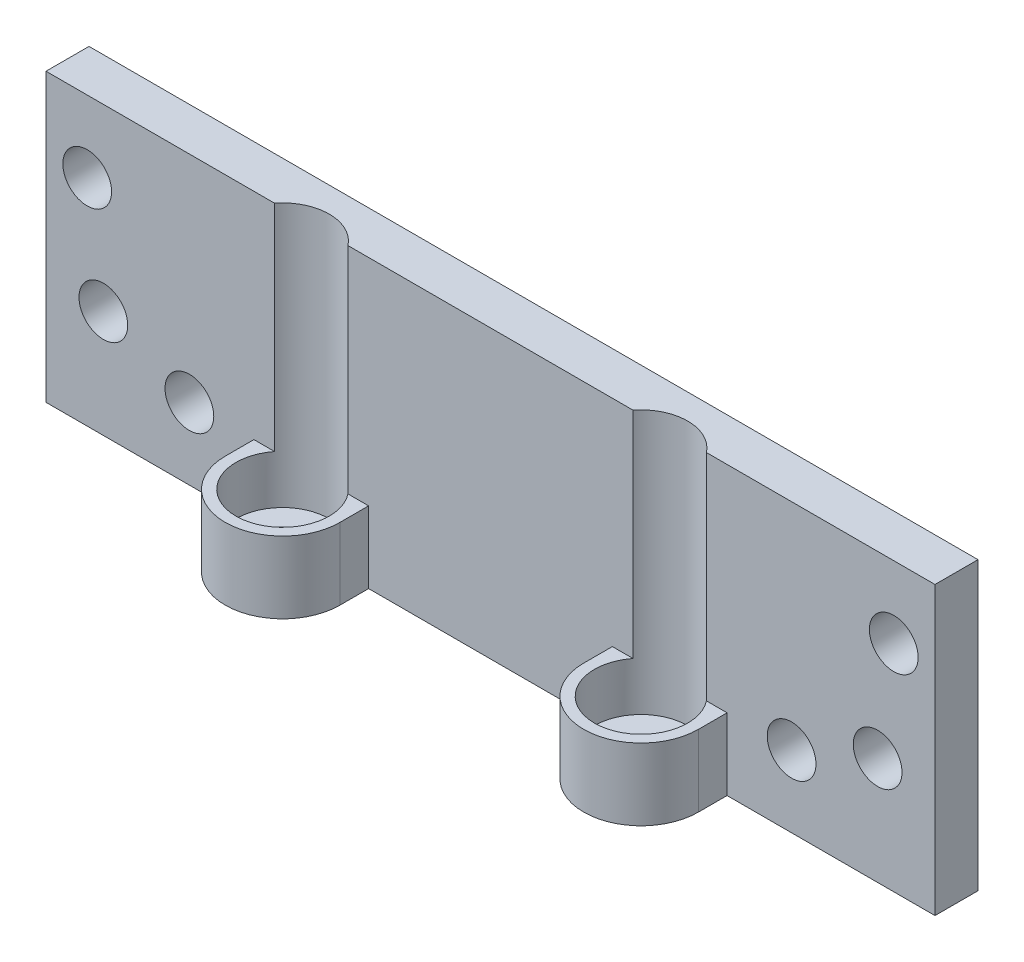
SolidWorks part; units mm, degrees
ref_plane "Front Plane" through (0, 0, 0) normal (0, 0, 1) x (1, 0, 0)
ref_plane "Top Plane" through (0, 0, 0) normal (0, 1, 0) x (1, 0, 0)
ref_plane "Right Plane" through (0, 0, 0) normal (1, 0, 0) x (0, 0, -1)
sketch "Sketch1" plane through (0, 0, 0) normal (0, 1, 0) x (1, 0, 0)
  line L0 (-31, -1.5) -> (-16.5, -1.5)
  line L2 (-31, -1.5) -> (-31, 1.5)
  line L3 (-31, 1.5) -> (31, 1.5)
  line L4 (31, -1.5) -> (31, 1.5)
  line L5 (-31, -1.5) -> (31, 1.5) construction
  line L6 (-31, 1.5) -> (31, -1.5) construction
  line L7 (-16.5, -1.5) -> (-16.5, -3.5)
  line L8 (-8.5, -3.5) -> (-8.5, -1.5)
  line L9 (-8.5, -1.5) -> (8.5, -1.5)
  line L10 (8.5, -1.5) -> (8.5, -3.5)
  line L11 (16.5, -3.5) -> (16.5, -1.5)
  line L12 (16.5, -1.5) -> (31, -1.5)
  arc A0 (-16.5, -3.5) -> (-8.5, -3.5) centre (-12.5, -3.5) ccw
  arc A1 (8.5, -3.5) -> (16.5, -3.5) centre (12.5, -3.5) ccw
  point P0 (0, 0)
  dimension "D1" = 62
  dimension "D2" = 3
  dimension "D3" = 25
  dimension "D4" = 5
  dimension "D5" = 8
extrude "Boss-Extrude1" add sketch "Sketch1" along normal blind 20
sketch "Sketch2" plane through (0, 20, 0) normal (0, 1, 0) x (1, 0, 0)
  line L1 (-16.5, -1.5) -> (16.5, -1.5)
  line L2 (-16.5, -1.5) -> (-16.5, -7.5)
  line L3 (-16.5, -7.5) -> (16.5, -7.5)
  line L4 (16.5, -1.5) -> (16.5, -7.5)
  arc A0 (8.5, -3.5) -> (16.5, -3.5) centre (12.5, -3.5) ccw construction
extrude "Cut-Extrude1" cut sketch "Sketch2" against normal blind 15
hole_wizard "CBORE for M3 Hex Socket Head Cap Screw1" positions "Sketch3" profile "Sketch4" counterbore size "M3" standard "DIN"
sketch "Sketch3" plane through (0, 5, 0) normal (0, 1, 0) x (1, 0, 0)
  point P0 (-12.5, -3.5)
  point P3 (12.5, -3.5)
sketch "Sketch4" plane through (-12.5, 5, 3.5) normal (1, 0, 0) x (0, 0, 1)
  line L0 (0, 0) -> (0, 5)
  line L1 (0, 5) -> (1.6, 5)
  line L3 (1.6, 5) -> (1.6, 3.4)
  line L4 (1.6, 3.4) -> (3.25, 3.4)
  line L5 (3.25, 3.4) -> (3.25, 0)
  line L7 (3.25, 0) -> (0, 0)
  line L11 (0, -6.35) -> (0, 107.95) construction
  dimension "Thru Hole Dia." = 3.2
  dimension "Thru Hole Depth" = 5
  dimension "C'Bore Dia." = 6.5
  dimension "C'Bore Depth" = 3.4
sketch "Sketch5" plane through (0, 5, 0) normal (0, -1, 0) x (1, 0, 0)
  line L1 (-9.9383, 1.5) -> (-15.0617, 1.5)
  line L2 (-9.9383, 1.5) -> (-15.0617, 1.5)
  line L3 (15.0617, 1.5) -> (9.9383, 1.5)
  line L4 (15.0617, 1.5) -> (9.9383, 1.5)
  arc A1 (-15.0617, 1.5) -> (-9.9383, 1.5) centre (-12.5, 3.5) ccw
  arc A2 (-15.0617, 1.5) -> (-9.9383, 1.5) centre (-12.5, 3.5) ccw
  arc A3 (9.9383, 1.5) -> (15.0617, 1.5) centre (12.5, 3.5) ccw
  arc A4 (9.9383, 1.5) -> (15.0617, 1.5) centre (12.5, 3.5) ccw
  dimension "D1" = 0
  dimension "D2" = 0
extrude "Cut-Extrude2" cut sketch "Sketch5" against normal up to surface (15 mm away) up to face at (0, 20, 0)
hole_wizard "M3 Clearance Hole1" positions "Sketch9" profile "Sketch10" hole size "M3" standard "DIN" end condition up to next
sketch "Sketch9" plane through (0, 0, 1.5) normal (0, 0, 1) x (1, 0, 0)
  line L0 (-8.5, 0) -> (8.5, 0) construction
  line L1 (-31, 0) -> (-16.5, 0) construction
  line L2 (16.5, 0) -> (31, 0) construction
  point P0 (-28.125, 15)
  point P2 (28.125, 15)
  point P10 (-21, 5)
  point P12 (21, 5)
  point P18 (-27, 7.5)
  point P20 (27, 7.5)
  dimension "D1" = 56.25
  dimension "D2" = 28.125
  dimension "D3" = 15
  dimension "D4" = 5
  dimension "D5" = 42
  dimension "D6" = 21
  dimension "D7" = 7.5
  dimension "D8" = 54
  dimension "D9" = 27
sketch "Sketch10" plane through (-28.125, 15, 1.5) normal (1, 0, 0) x (0, -1, 0)
  line L0 (0, 0) -> (0, 3)
  line L1 (0, 3) -> (1.7, 3)
  line L2 (1.7, 3) -> (1.7, 0)
  line L5 (1.7, 0) -> (0, 0)
  line L11 (0, -6.35) -> (0, 107.95) construction
  dimension "Thru Hole Dia." = 3.4
  dimension "Thru Hole Depth" = 3
